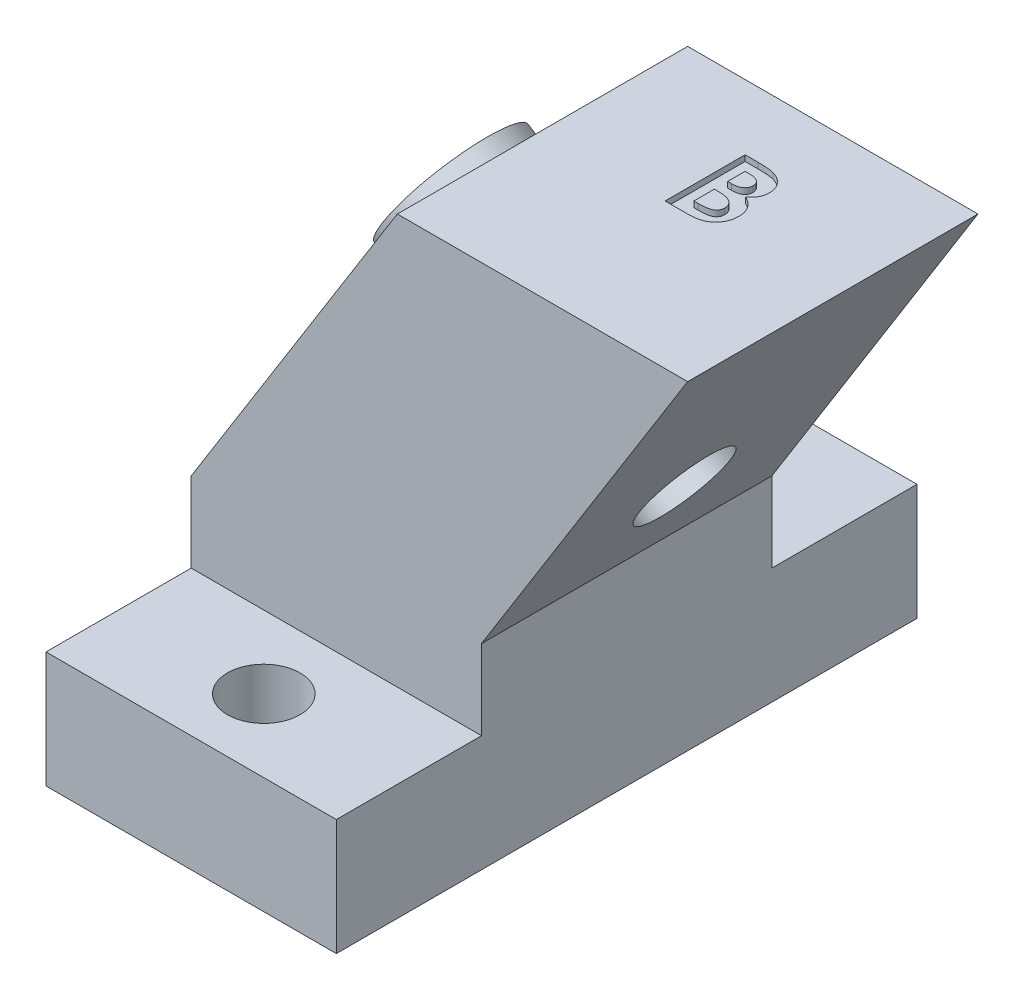
SolidWorks part; units mm, degrees
ref_plane "Front Plane" through (0, 0, 0) normal (0, 0, 1) x (1, 0, 0)
ref_plane "Top Plane" through (0, 0, 0) normal (0, 1, 0) x (1, 0, 0)
ref_plane "Right Plane" through (0, 0, 0) normal (1, 0, 0) x (0, 0, -1)
sketch "Sketch7" plane through (0, 0, 0) normal (0, 0, 1) x (1, 0, 0)
  line L0 (0, 8.5714) -> (12.192, 28.0826)
  line L1 (0, 0) -> (12.7, 0)
  line L2 (0, 0) -> (0, 8.5714)
  line L4 (12.7, 0) -> (12.7, 8.5714)
  line L5 (12.7, 8.5714) -> (24.892, 28.0826)
  line L6 (12.192, 28.0826) -> (24.892, 28.0826)
  line L7 (12.7, 8.5714) -> (31.8633, 8.5714) construction
  line L8 (6.096, 18.327) -> (5.019, 19) construction
  point P11 (18.796, 18.327)
  dimension "D1" = 58
  dimension "D2" = 1.27
  dimension "D3" = 6.096
  dimension "D4" = 12.7
  dimension "D5" = 19
extrude "Boss-Extrude3" add sketch "Sketch7" along normal blind 12.7
sketch "Sketch8" plane through (-3.8519, 2.407, 0) normal (-0.848, 0.5299, 0) x (0, 0, 1)
  line L0 (6.35, 30.2762) -> (6.35, 7.2689) construction
  line L1 (12.7, 30.2762) -> (0, 30.2762) construction
  line L2 (12.7, 7.2689) -> (0, 7.2689) construction
  circle A0 centre (6.35, 18.7726) radius 2
  point P9 (6.35, 18.7726)
  dimension "D1" = 4
extrude "Cut-Extrude5" cut sketch "Sketch8" against normal blind 12.7
sketch "Sketch9" plane through (0, 0, 12.7) normal (0, 0, 1) x (1, 0, 0)
  line L0 (21.7177, 23.0026) -> (9.0177, 23.0026)
  line L6 (12.7, 8.5714) -> (24.892, 28.0826) construction
  line L8 (12.192, 28.0826) -> (24.892, 28.0826)
  line L9 (24.892, 28.0826) -> (21.7177, 23.0026)
  line L11 (12.192, 28.0826) -> (0, 8.5714) construction
  line L12 (9.0177, 23.0026) -> (12.192, 28.0826)
  point P4 (9.2157, 23.3196)
  dimension "D1" = 5.08
extrude "Cut-Extrude7" cut sketch "Sketch9" against normal blind 12.7
sketch "Sketch10" plane through (0, 0, 12.7) normal (0, 0, 1) x (1, 0, 0)
  line L0 (12.7, 0) -> (12.7, 8.5714) construction
  line L1 (0, 0) -> (12.7, 0)
  line L2 (0, 0) -> (0, 5.08)
  line L3 (0, 5.08) -> (12.7, 5.08)
  line L4 (12.7, 0) -> (12.7, 5.08)
  dimension "D1" = 5.08
extrude "Boss-Extrude4" add sketch "Sketch10" along normal blind 6.35
sketch "Sketch11" plane through (0, 5.08, 0) normal (0, 1, 0) x (1, 0, 0)
  line L0 (0, -15.875) -> (12.7, -15.875) construction
  line L1 (0, -19.05) -> (0, -12.7) construction
  line L2 (12.7, -19.05) -> (12.7, -12.7) construction
  circle A0 centre (6.35, -15.875) radius 1.5875
  point P10 (6.35, -15.875)
  dimension "D1" = 3.175
extrude "Cut-Extrude8" cut sketch "Sketch11" against normal blind 12.7
ref_plane "Plane2" through (0, 0, 6.35) normal (0, 0, 1) x (1, 0, 0)
mirror "Mirror2" about plane through (0, 0, 6.35) normal (0, 0, 1) of "Boss-Extrude4", "Cut-Extrude8"
sketch "Sketch12" plane through (0, 0, 6.35) normal (0, 0, 1) x (1, 0, 0)
  line L4 (3.5787, 17.5416) -> (16.2895, 14.3158) construction
  line L5 (5.0362, 16.6309) -> (14.1698, 10.9236) construction
sketch "Sketch13" plane through (-3.8519, 2.407, 0) normal (-0.848, 0.5299, 0) x (0, 0, 1)
  line L0 (6.35, 16.7726) -> (6.35, 20.7726) construction
  circle A0 centre (6.35, 18.7726) radius 3
  circle A1 centre (6.35, 18.7726) radius 2
  circle A2 centre (6.35, 18.7726) radius 2 construction
  dimension "D1" = 6
extrude "Boss-Extrude5" add sketch "Sketch13" along normal blind 1.27
sketch "Sketch14" plane through (-4.929, 3.08, 0) normal (-0.848, 0.5299, 0) x (0, 0, 1)
  line L0 (6.35, 21.7726) -> (6.35, 15.7726) construction
  line L1 (6.35, -9.8575) -> (6.35, 9.8575) construction
  circle A0 centre (6.35, 18.7726) radius 3 construction
  point P6 (6.35, 18.7726)
sketch "Sketch15" plane through (0, 0, 6.35) normal (0, 0, 1) x (1, 0, 0)
  line L0 (5.019, 19) -> (5.019, 25.8408) construction
sketch "Sketch17" plane through (0, 23.0026, 0) normal (0, 1, 0) x (1, 0, 0)
  line L0 (9.0177, -6.35) -> (21.7177, -6.35) construction
  line L1 (9.0177, 0) -> (9.0177, -12.7) construction
  line L2 (-9.8575, -6.35) -> (9.8575, -6.35) construction
  line L3 (21.7177, 0) -> (21.7177, -12.7) construction
  text T0 "<b>B</b>\r\n"
  point P6 (29.5054, -6.35)
  point P7 (0, 0)
extrude "Cut-Extrude10" cut sketch "Sketch17" against normal blind 0.254
